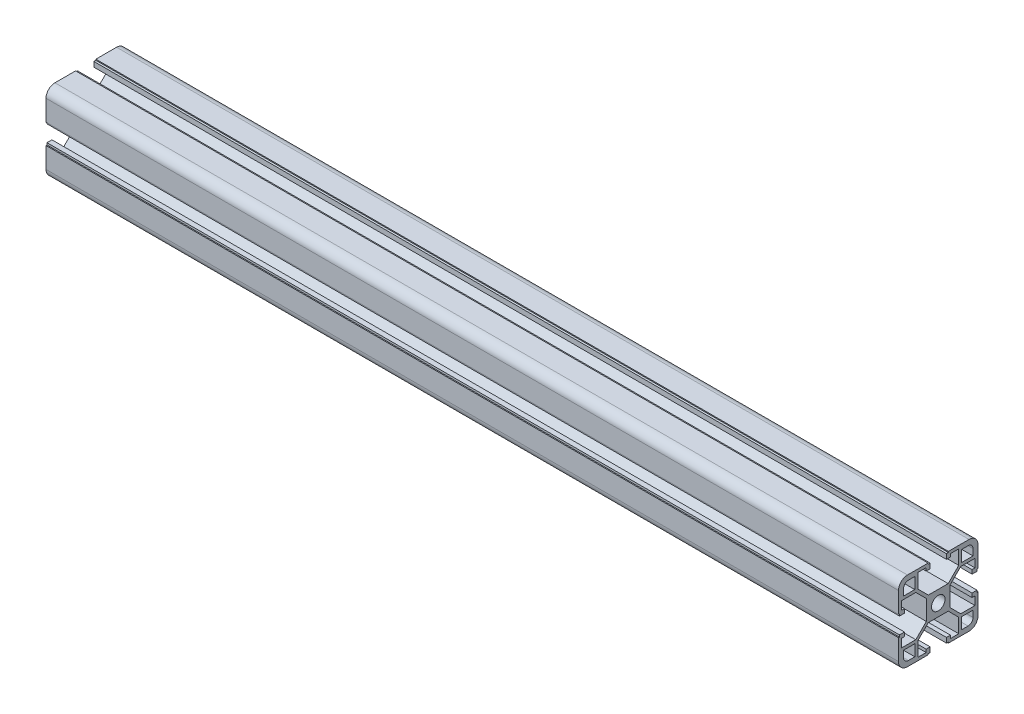
SolidWorks part; units mm, degrees
ref_plane "前视基准面" through (0, 0, 0) normal (0, 0, 1) x (1, 0, 0)
ref_plane "上视基准面" through (0, 0, 0) normal (0, 1, 0) x (1, 0, 0)
ref_plane "右视基准面" through (0, 0, 0) normal (1, 0, 0) x (0, 0, -1)
sketch "草图1" plane through (0, 0, 0) normal (0, 1, 0) x (1, 0, 0)
  line L0 (-12.1681, 0) -> (416.8319, 0)
  dimension "D1" = 429
other "铝型材 40 X 40L X R4.5(1)"
ref_plane "基准面1" through (-12.1681, 0, 0) normal (1, 0, 0) x (0, 0, -1)
sketch "Sketch1" plane through (-12.1681, 0, 0) normal (1, 0, 0) x (0, 0, -1)
  line L0 (-5.1, 20) -> (-5.1, 19.5)
  line L1 (-5.1, 19.5) -> (-4.1, 19.5)
  line L2 (-4.1, 19.5) -> (-4.1, 17)
  line L3 (-6.1, 18.5) -> (-10.3, 18.5)
  line L4 (-15.5, -20) -> (-5.1, -20)
  line L5 (-20, -15.5) -> (-20, -5.1)
  line L6 (15.5, 20) -> (5.1, 20)
  line L7 (20, 15.5) -> (20, 5.1)
  line L8 (0, 14.8756) -> (0, 0) construction
  line L9 (0, 0) -> (14.1675, 0) construction
  line L10 (-10.3, 18.5) -> (-10.3, 11.3)
  line L11 (-10.3, 11.3) -> (-5, 6)
  line L12 (-5, 6) -> (5, 6)
  line L13 (10.3, 11.3) -> (5, 6)
  line L14 (10.3, 18.5) -> (10.3, 11.3)
  line L15 (6.1, 18.5) -> (10.3, 18.5)
  line L16 (4.1, 19.5) -> (4.1, 17)
  line L17 (5.1, 19.5) -> (4.1, 19.5)
  line L18 (5.1, 20) -> (5.1, 19.5)
  line L19 (-5.1, 20) -> (-15.5, 20)
  line L20 (20, 5.1) -> (19.5, 5.1)
  line L21 (11.8, 17.5) -> (15, 17.5)
  line L22 (11.8, 17.5) -> (11.8, 11.8)
  line L23 (11.8, 11.8) -> (17.5, 11.8)
  line L24 (17.5, 15) -> (17.5, 11.8)
  line L25 (19.5, 5.1) -> (19.5, 4.1)
  line L26 (19.5, 4.1) -> (17, 4.1)
  line L27 (17, 6.1) -> (17, 4.1)
  line L28 (18.5, 6.1) -> (17, 6.1)
  line L29 (18.5, 6.1) -> (18.5, 10.3)
  line L30 (18.5, 10.3) -> (11.3, 10.3)
  line L31 (11.3, 10.3) -> (6, 5)
  line L32 (6, 5) -> (6, -5)
  line L33 (11.3, -10.3) -> (6, -5)
  line L34 (18.5, -10.3) -> (11.3, -10.3)
  line L35 (18.5, -6.1) -> (18.5, -10.3)
  line L36 (18.5, -6.1) -> (17, -6.1)
  line L37 (17, -4.1) -> (17, -6.1)
  line L38 (19.5, -4.1) -> (17, -4.1)
  line L39 (19.5, -5.1) -> (19.5, -4.1)
  line L40 (20, -5.1) -> (19.5, -5.1)
  line L41 (5.1, -20) -> (5.1, -19.5)
  line L42 (5.1, -19.5) -> (4.1, -19.5)
  line L43 (4.1, -19.5) -> (4.1, -17)
  line L44 (6.1, -17) -> (4.1, -17)
  line L45 (6.1, -18.5) -> (6.1, -17)
  line L46 (6.1, -18.5) -> (10.3, -18.5)
  line L47 (10.3, -18.5) -> (10.3, -11.3)
  line L48 (10.3, -11.3) -> (5, -6)
  line L49 (5, -6) -> (-5, -6)
  line L50 (-10.3, -11.3) -> (-5, -6)
  line L51 (-10.3, -18.5) -> (-10.3, -11.3)
  line L52 (-6.1, -18.5) -> (-10.3, -18.5)
  line L53 (-6.1, -18.5) -> (-6.1, -17)
  line L54 (-4.1, -17) -> (-6.1, -17)
  line L55 (-4.1, -19.5) -> (-4.1, -17)
  line L56 (-5.1, -19.5) -> (-4.1, -19.5)
  line L57 (-5.1, -20) -> (-5.1, -19.5)
  line L58 (-20, -5.1) -> (-19.5, -5.1)
  line L59 (5.1, -20) -> (15.5, -20)
  line L60 (-20, 5.1) -> (-20, 15.5)
  line L61 (-19.5, -5.1) -> (-19.5, -4.1)
  line L62 (-6.1, 18.5) -> (-6.1, 17)
  line L63 (-6.1, 17) -> (-4.1, 17)
  line L64 (6.1, 18.5) -> (6.1, 17)
  line L65 (4.1, 17) -> (6.1, 17)
  line L66 (-19.5, -4.1) -> (-17, -4.1)
  line L67 (-15, 17.5) -> (-11.8, 17.5)
  line L68 (-17.5, 15) -> (-17.5, 11.8)
  line L69 (-17.5, 11.8) -> (-11.8, 11.8)
  line L70 (-11.8, 17.5) -> (-11.8, 11.8)
  line L71 (-17, -6.1) -> (-17, -4.1)
  line L72 (-18.5, -6.1) -> (-17, -6.1)
  line L73 (-18.5, -6.1) -> (-18.5, -10.3)
  line L74 (-18.5, -10.3) -> (-11.3, -10.3)
  line L75 (-11.3, -10.3) -> (-6, -5)
  line L76 (-6, -5) -> (-6, 5)
  line L77 (-11.3, 10.3) -> (-6, 5)
  line L78 (-18.5, 10.3) -> (-11.3, 10.3)
  line L79 (-18.5, 6.1) -> (-18.5, 10.3)
  line L80 (-18.5, 6.1) -> (-17, 6.1)
  line L81 (-17, 4.1) -> (-17, 6.1)
  line L82 (-19.5, 4.1) -> (-17, 4.1)
  line L83 (-19.5, 5.1) -> (-19.5, 4.1)
  line L84 (-20, 5.1) -> (-19.5, 5.1)
  line L85 (20, -5.1) -> (20, -15.5)
  line L87 (-17.5, -11.8) -> (-11.8, -11.8)
  line L88 (-17.5, -11.8) -> (-17.5, -15)
  line L89 (-15, -17.5) -> (-11.8, -17.5)
  line L90 (-11.8, -11.8) -> (-11.8, -17.5)
  line L91 (11.8, -11.8) -> (17.5, -11.8)
  line L92 (11.8, -11.8) -> (11.8, -17.5)
  line L93 (11.8, -17.5) -> (15, -17.5)
  line L94 (17.5, -11.8) -> (17.5, -15)
  circle A0 centre (0, 0) radius 3.4
  arc A1 (-20, 15.5) -> (-15.5, 20) centre (-15.5, 15.5) cw
  arc A2 (20, 15.5) -> (15.5, 20) centre (15.5, 15.5) ccw
  arc A3 (-15.5, -20) -> (-20, -15.5) centre (-15.5, -15.5) cw
  arc A4 (15.5, -20) -> (20, -15.5) centre (15.5, -15.5) ccw
  arc A5 (-15, 17.5) -> (-17.5, 15) centre (-15, 15) ccw
  arc A6 (17.5, 15) -> (15, 17.5) centre (15, 15) ccw
  arc A7 (17.5, -15) -> (15, -17.5) centre (15, -15) cw
  arc A8 (-17.5, -15) -> (-15, -17.5) centre (-15, -15) ccw
  point P2 (0, 10)
  point P4 (0, 0)
  point P5 (-20, -20)
  point P6 (20, -20)
  point P7 (20, 20)
  point P8 (-20, 20)
  point P36 (-20, 20)
  point P39 (20, 20)
  point P121 (0, 0)
  dimension "D1" = 20.6
  dimension "D2" = 40
  dimension "D3" = 8.2
  dimension "D4" = 10.2
  dimension "D5" = 14
  dimension "D6" = 6.8
  dimension "D7" = 4.5
  dimension "D8" = 45
  dimension "D12" = 2.5
  dimension "D13" = 5.7
  dimension "D14" = 1.5
  dimension "D18" = 2.5
  dimension "D19" = 2.5
  dimension "D15" = 2.5
  dimension "D9" = 0.5
  dimension "D10" = 1.5
  dimension "D11" = 10
  dimension "D16" = 3
  dimension "D17" = 2
  dimension "D20" = 1.5
  dimension "D21" = 2.5
